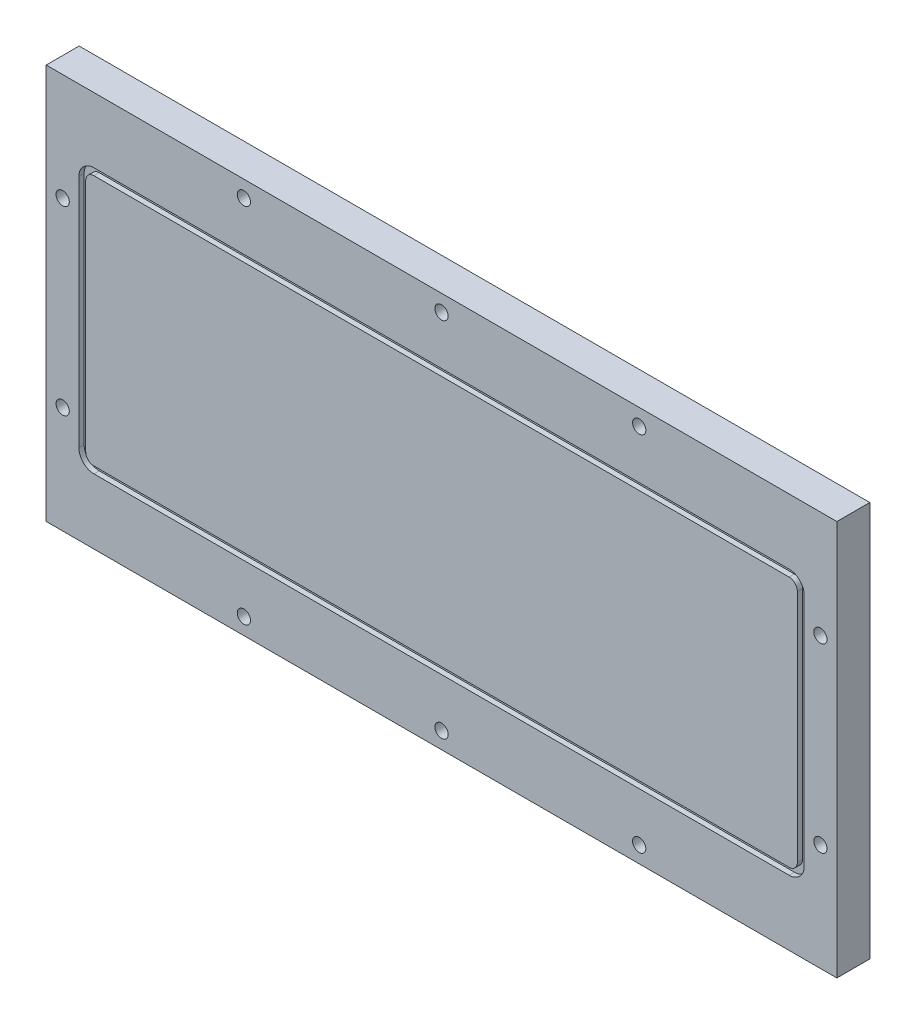
SolidWorks part; units mm, degrees
ref_plane "Front Plane" through (0, 0, 0) normal (0, 0, 1) x (1, 0, 0)
ref_plane "Top Plane" through (0, 0, 0) normal (0, 1, 0) x (1, 0, 0)
ref_plane "Right Plane" through (0, 0, 0) normal (1, 0, 0) x (0, 0, -1)
ref_plane "Plane1" through (0, 0, 12.7) normal (0, 0, 1) x (1, 0, 0)
sketch "Sketch1" plane through (0, 0, 12.7) normal (0, 0, 1) x (1, 0, 0)
  line L0 (152.4, -76.2) -> (152.4, 76.2)
  line L1 (152.4, 76.2) -> (-152.4, 76.2)
  line L2 (-152.4, 76.2) -> (-152.4, -76.2)
  line L3 (-152.4, -76.2) -> (152.4, -76.2)
  dimension "D1" = 152.4
  dimension "D2" = 76.2
  dimension "D3" = 304.8
  dimension "D4" = 152.4
extrude "Boss-Extrude1" add sketch "Sketch1" against normal blind 12.7
sketch "Sketch2" plane through (0, 0, 12.7) normal (0, 0, 1) x (1, 0, 0)
  line L0 (-139.8016, -51.0921) -> (139.8016, -51.0921)
  line L1 (139.8016, -51.0921) -> (139.8016, 51.0921)
  line L2 (139.8016, 51.0921) -> (-139.8016, 51.0921)
  line L3 (-139.8016, 51.0921) -> (-139.8016, -51.0921)
extrude "Cut-Extrude1" cut sketch "Sketch2" against normal blind 2.032
sketch "Sketch3" plane through (0, 0, 10.668) normal (0, 0, 1) x (1, 0, 0)
  line L0 (137.16, 48.4505) -> (137.16, -48.4505)
  line L1 (137.16, -48.4505) -> (-137.16, -48.4505)
  line L2 (-137.16, -48.4505) -> (-137.16, 48.4505)
  line L3 (-137.16, 48.4505) -> (137.16, 48.4505)
extrude "Boss-Extrude2" add sketch "Sketch3" along normal blind 2.032
hole_wizard "1/4-20 Tapped Hole1" positions "Sketch5" profile "Sketch4" tap size "1/4-20" standard "ANSI Inch"
sketch "Sketch5" plane through (0, 0, 0) normal (0, 0, -1) x (-1, 0, 0)
  point P0 (120.65, -38.1)
  point P1 (-120.65, 38.1)
  point P2 (120.65, 38.1)
  point P3 (-120.65, -38.1)
sketch "Sketch4" plane through (-120.65, -38.1, 0) normal (1, 0, 0) x (0, 1, 0)
  line L0 (0, 0) -> (0, 9.1538)
  line L1 (0, 9.1538) -> (2.5527, 7.62)
  line L2 (2.5527, 7.62) -> (2.5527, 0)
  line L5 (2.5527, 0) -> (0, 0)
  line L10 (0, 9.1538) -> (-2.5527, 7.62) construction
  line L11 (0, -6.35) -> (0, 107.95) construction
  dimension "Tap Drill Dia." = 5.1054
  dimension "Tap Drill Depth" = 7.62
  dimension "Drill Angle" = 118
hole_wizard "M3.5 Clearance Hole1" positions "Sketch7" profile "Sketch6" hole size "M3.5" standard "ANSI Metric"
sketch "Sketch7" plane through (0, 0, 0) normal (0, 0, -1) x (-1, 0, 0)
  point P0 (-146.05, 44.45)
  point P1 (-146.05, -44.45)
  point P2 (-146.05, 0)
  point P3 (146.05, -44.45)
  point P4 (146.05, 44.45)
  point P5 (146.05, 0)
sketch "Sketch6" plane through (146.05, 44.45, 0) normal (1, 0, 0) x (0, 1, 0)
  line L0 (0, 0) -> (0, 9.0148)
  line L1 (0, 9.0148) -> (1.8986, 7.874)
  line L2 (1.8986, 7.874) -> (1.8986, 0)
  line L5 (1.8986, 0) -> (0, 0)
  line L10 (0, 9.0148) -> (-1.8986, 7.874) construction
  line L11 (0, -6.35) -> (0, 107.95) construction
  dimension "Hole Dia." = 3.7973
  dimension "Hole Depth" = 7.874
  dimension "Drill Angle" = 118
hole_wizard "#6-32 Tapped Hole1" positions "Sketch9" profile "Sketch8" tap size "#6-32" standard "ANSI Inch"
sketch "Sketch9" plane through (0, 0, 0) normal (0, 0, -1) x (-1, 0, 0)
  point P0 (0, 12.7)
sketch "Sketch8" plane through (0, 12.7, 0) normal (1, 0, 0) x (0, 1, 0)
  line L0 (0, 0) -> (0, 10.2005)
  line L1 (0, 10.2005) -> (1.3525, 9.3878)
  line L2 (1.3525, 9.3878) -> (1.3525, 0)
  line L5 (1.3525, 0) -> (0, 0)
  line L10 (0, 10.2005) -> (-1.3526, 9.3878) construction
  line L11 (0, -6.35) -> (0, 107.95) construction
  dimension "Tap Drill Dia." = 2.7051
  dimension "Tap Drill Depth" = 9.3878
  dimension "Drill Angle" = 118
hole_wizard "CBORE for #10 Socket Head Cap Screw1" positions "Sketch11" profile "Sketch10" counterbore size "#10" standard "ANSI Inch" end condition through all
sketch "Sketch11" plane through (0, 0, 0) normal (0, 0, -1) x (-1, 0, 0)
  line L0 (-152.4, 76.2) -> (152.4, 76.2) construction
  line L1 (-152.4, 76.2) -> (152.4, 76.2) construction
  line L2 (152.4, 76.2) -> (152.4, -76.2) construction
  point P1 (146.05, 34.925)
  point P2 (0, 69.85)
  point P6 (76.2, 69.85)
  point P13 (0, 76.2)
  dimension "D1" = 6.35
  dimension "D2" = 6.35
  dimension "D3" = 6.35
  dimension "D4" = 41.275
  dimension "D5" = 76.2
sketch "Sketch10" plane through (-146.05, 34.925, 0) normal (1, 0, 0) x (0, 1, 0)
  line L0 (0, 0) -> (0, 12.7)
  line L1 (0, 12.7) -> (2.5527, 12.7)
  line L3 (2.5527, 12.7) -> (2.5527, 4.826)
  line L4 (2.5527, 4.826) -> (4.7625, 4.826)
  line L5 (4.7625, 4.826) -> (4.7625, 0)
  line L7 (4.7625, 0) -> (0, 0)
  line L11 (0, -6.35) -> (0, 107.95) construction
  dimension "Thru Hole Dia." = 5.1054
  dimension "Thru Hole Depth" = 12.7
  dimension "C'Bore Dia." = 9.525
  dimension "C'Bore Depth" = 4.826
hole_wizard "M3.5 Clearance Hole2" positions "Sketch13" profile "Sketch12" hole size "M3.5" standard "ANSI Metric"
sketch "Sketch13" plane through (0, 63.5, 0) normal (0, 1, 0) x (1, 0, 0)
  point P0 (101.6, -6.35)
  point P1 (-101.6, -6.35)
sketch "Sketch12" plane through (101.6, 63.5, 6.35) normal (1, 0, 0) x (0, 0, 1)
  line L0 (0, 0) -> (0, 14.0948)
  line L1 (0, 14.0948) -> (1.8986, 12.954)
  line L2 (1.8986, 12.954) -> (1.8986, 0)
  line L5 (1.8986, 0) -> (0, 0)
  line L10 (0, 14.0948) -> (-1.8986, 12.954) construction
  line L11 (0, -6.35) -> (0, 107.95) construction
  dimension "Hole Dia." = 3.7973
  dimension "Hole Depth" = 12.954
  dimension "Drill Angle" = 118
hole_wizard "M3.5 Clearance Hole3" positions "Sketch15" profile "Sketch14" hole size "M3.5" standard "ANSI Metric"
sketch "Sketch15" plane through (0, -63.5, 0) normal (0, -1, 0) x (-1, 0, 0)
  point P0 (101.6, -6.35)
  point P1 (-101.6, -6.35)
sketch "Sketch14" plane through (-101.6, -63.5, 6.35) normal (1, 0, 0) x (0, 0, -1)
  line L0 (0, 0) -> (0, 14.0948)
  line L1 (0, 14.0948) -> (1.8986, 12.954)
  line L2 (1.8986, 12.954) -> (1.8986, 0)
  line L5 (1.8986, 0) -> (0, 0)
  line L10 (0, 14.0948) -> (-1.8986, 12.954) construction
  line L11 (0, -6.35) -> (0, 107.95) construction
  dimension "Hole Dia." = 3.7973
  dimension "Hole Depth" = 12.954
  dimension "Drill Angle" = 118
fillet "Fillet1" radius 3.175 4 edges at (137.16, 48.4505, 11.684) (137.16, -48.4505, 11.684) (-137.16, 48.4505, 11.684) (-137.16, -48.4505, 11.684)
fillet "Fillet2" radius 5.8166 4 edges at (-139.8016, 51.0921, 11.684) (-139.8016, -51.0921, 11.684) (139.8016, 51.0921, 11.684) (139.8016, -51.0921, 11.684)
mirror "Mirror1" about plane through (0, 0, 0) normal (1, 0, 0) of "CBORE for #10 Socket Head Cap Screw1"
mirror "Mirror2" about plane through (0, 0, 0) normal (0, 1, 0) of "Mirror1", "CBORE for #10 Socket Head Cap Screw1"
equation "\"D2@Sketch1\"=\"D1@Sketch1\"/2"
equation "\"D4@Sketch1\"=\"D3@Sketch1\"/2"
